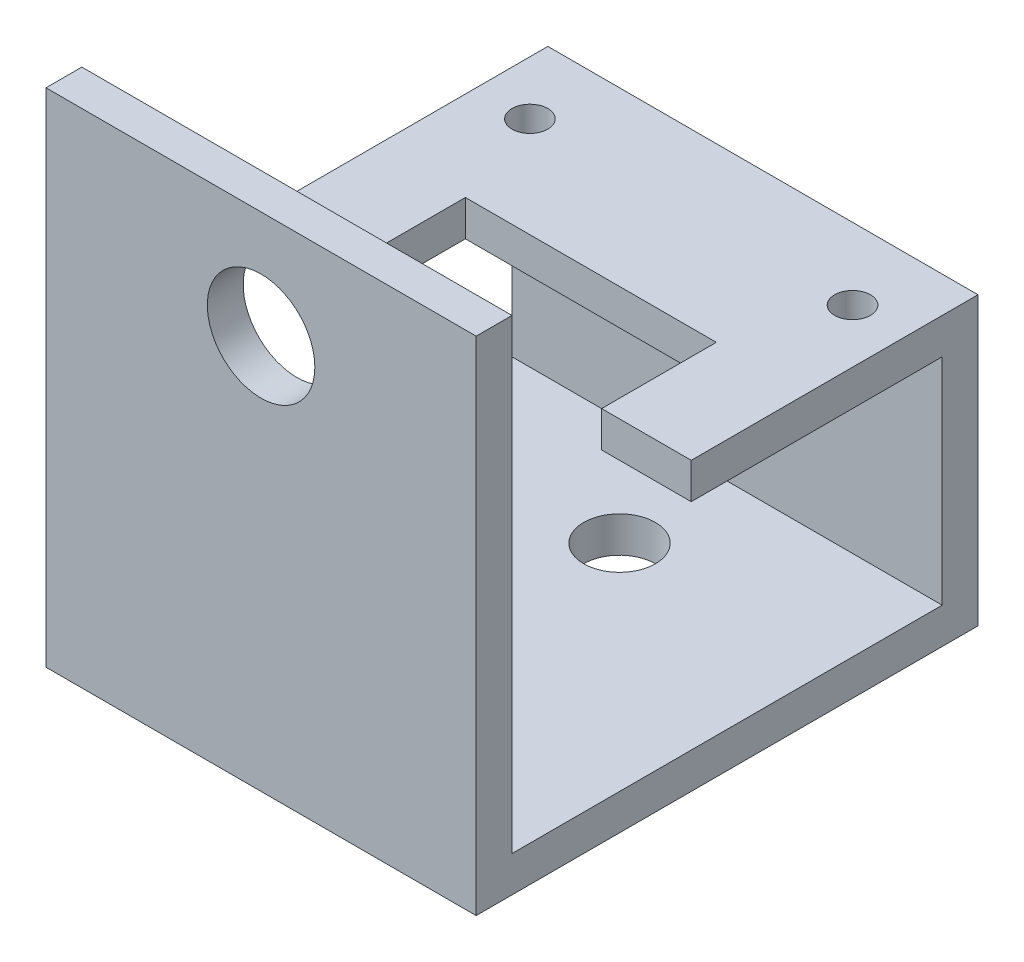
SolidWorks part; units mm, degrees
ref_plane "Front Plane" through (0, 0, 0) normal (0, 0, 1) x (1, 0, 0)
ref_plane "Top Plane" through (0, 0, 0) normal (0, 1, 0) x (1, 0, 0)
ref_plane "Right Plane" through (0, 0, 0) normal (1, 0, 0) x (0, 0, -1)
sketch "Sketch1" plane through (0, 0, 0) normal (1, 0, 0) x (0, 0, -1)
  line L0 (0, 0) -> (-38.1, 0)
  line L1 (-38.1, 0) -> (-38.1, 41.275)
  line L2 (-41.275, 41.275) -> (-38.1, 41.275)
  line L5 (-41.275, 41.275) -> (-41.275, -3.175)
  line L6 (-41.275, -3.175) -> (3.175, -3.175)
  line L7 (3.175, -3.175) -> (3.175, 22.225)
  line L8 (3.175, 22.225) -> (-22.225, 22.225)
  line L9 (-22.225, 22.225) -> (-22.225, 19.05)
  line L10 (-22.225, 19.05) -> (0, 19.05)
  line L11 (0, 19.05) -> (0, 0)
  dimension "D1" = 44.45
  dimension "D2" = 44.45
  dimension "D3" = 3.175
  dimension "D4" = 3.175
  dimension "D5" = 3.175
  dimension "D6" = 3.175
  dimension "D7" = 25.4
  dimension "D8" = 25.4
extrude "Boss-Extrude1" add sketch "Sketch1" along normal blind 38.1
sketch "Sketch2" plane through (0, 22.225, 0) normal (0, 1, 0) x (1, 0, 0)
  line L0 (38.1, -22.225) -> (0, -22.225) construction
  line L1 (30.1625, -22.225) -> (7.9375, -22.225)
  line L2 (30.1625, -22.225) -> (30.1625, -12.065)
  line L3 (30.1625, -12.065) -> (7.9375, -12.065)
  line L4 (7.9375, -22.225) -> (7.9375, -12.065)
  line L5 (38.1, 3.175) -> (38.1, -22.225) construction
  line L6 (0, 3.175) -> (0, -22.225) construction
  line L8 (38.1, 3.175) -> (0, 3.175) construction
  dimension "D1" = 7.9375
  dimension "D2" = 7.9375
  dimension "D3" = 15.24
extrude "Cut-Extrude1" cut sketch "Sketch2" against normal up to surface (3.175 mm away) up to face at (19.05, 19.05, 11.1125)
sketch "Sketch6" plane through (0, 22.225, 0) normal (0, 1, 0) x (1, 0, 0)
  line L0 (38.1, 3.175) -> (0, 3.175) construction
  circle A0 centre (33.3375, -3.175) radius 1.5875
  circle A1 centre (4.7625, -3.175) radius 1.5875
  point P10 (19.05, 3.175)
  dimension "D4" = 3.175
  dimension "D5" = 3.175
  dimension "D1" = 28.575
  dimension "D2" = 6.35
  dimension "D3" = 14.2875
extrude "Cut-Extrude2" cut sketch "Sketch6" against normal up to surface (3.175 mm away) up to face at (19.05, 19.05, 14.1287)
sketch "Sketch7" plane through (0, 0, 41.275) normal (0, 0, 1) x (1, 0, 0)
  line L0 (38.1, -3.175) -> (0, -3.175) construction
  circle A0 centre (19.05, 31.75) radius 4.7625
  point P0 (19.05, -3.175)
  dimension "D2" = 9.525
  dimension "D1" = 34.925
extrude "Cut-Extrude3" cut sketch "Sketch7" against normal up to surface (3.175 mm away) up to face at (19.05, 20.6375, 38.1)
sketch "Sketch10" plane through (0, -3.175, 0) normal (0, -1, 0) x (-1, 0, 0)
  line L0 (-38.1, 3.175) -> (0, 3.175) construction
  line L1 (-19.05, 3.175) -> (-19.05, -41.275) construction
  line L2 (-38.1, -41.275) -> (0, -41.275) construction
  point P0 (-19.05, 3.175)
hole_wizard "1/4 (0.25) Diameter Hole1" positions "Sketch13" profile "Sketch12" hole size "1/4" standard "ANSI Inch"
sketch "Sketch13" plane through (0, -3.175, 0) normal (0, -1, 0) x (-1, 0, 0)
  line L0 (0, -41.275) -> (0, 3.175) construction
  line L1 (-38.1, -41.275) -> (0, -41.275) construction
  point P0 (-19.05, -28.575)
  point P2 (-19.05, -9.525)
  dimension "D1" = 19.05
  dimension "D2" = 19.05
  dimension "D3" = 12.7
sketch "Sketch12" plane through (19.05, -3.175, 28.575) normal (1, 0, 0) x (0, 0, -1)
  line L0 (0, 0) -> (0, 5.0817)
  line L1 (0, 5.0817) -> (3.175, 3.174)
  line L2 (3.175, 3.174) -> (3.175, 0)
  line L5 (3.175, 0) -> (0, 0)
  line L10 (0, 5.0817) -> (-3.175, 3.174) construction
  line L11 (0, -6.35) -> (0, 107.95) construction
  dimension "Hole Dia." = 6.35
  dimension "Hole Depth" = 3.174
  dimension "Drill Angle" = 118
